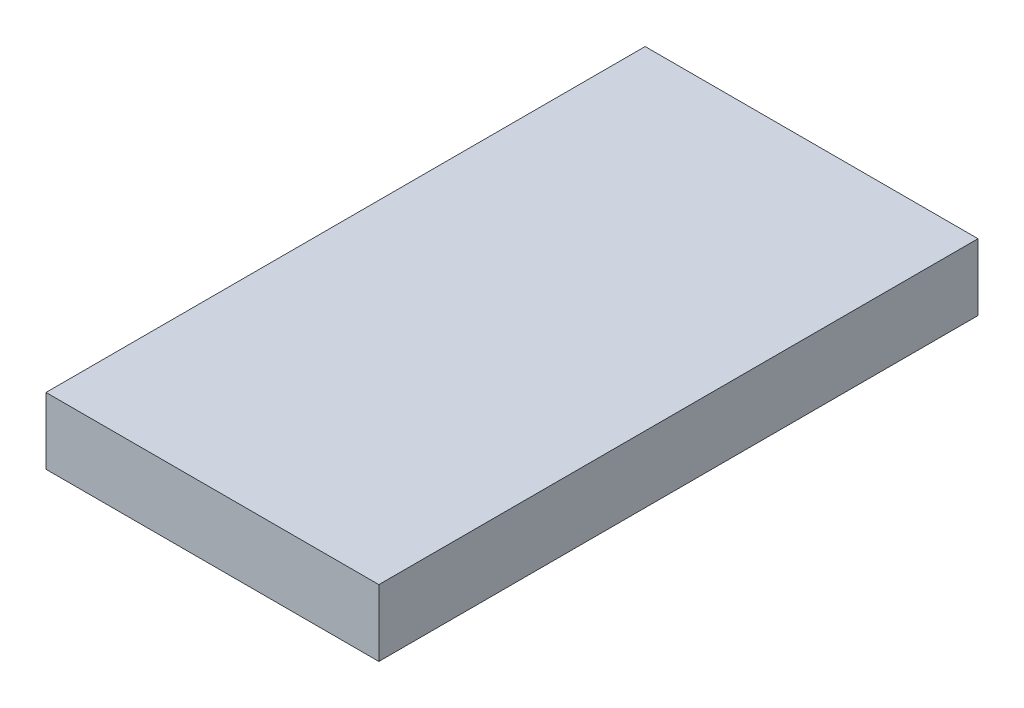
SolidWorks part; units mm, degrees
ref_plane "Front Plane" through (0, 0, 0) normal (0, 0, 1) x (1, 0, 0)
ref_plane "Top Plane" through (0, 0, 0) normal (0, 1, 0) x (1, 0, 0)
ref_plane "Right Plane" through (0, 0, 0) normal (1, 0, 0) x (0, 0, -1)
sketch "Sketch1" plane through (0, 0, 0) normal (0, 1, 0) x (1, 0, 0)
  line L1 (0, 0) -> (63.5, 0)
  line L2 (0, 0) -> (0, 114.3)
  line L3 (0, 114.3) -> (63.5, 114.3)
  line L4 (63.5, 0) -> (63.5, 114.3)
  dimension "D1" = 114.3
  dimension "D2" = 63.5
extrude "Extrude1" add sketch "Sketch1" along normal blind 12.7
